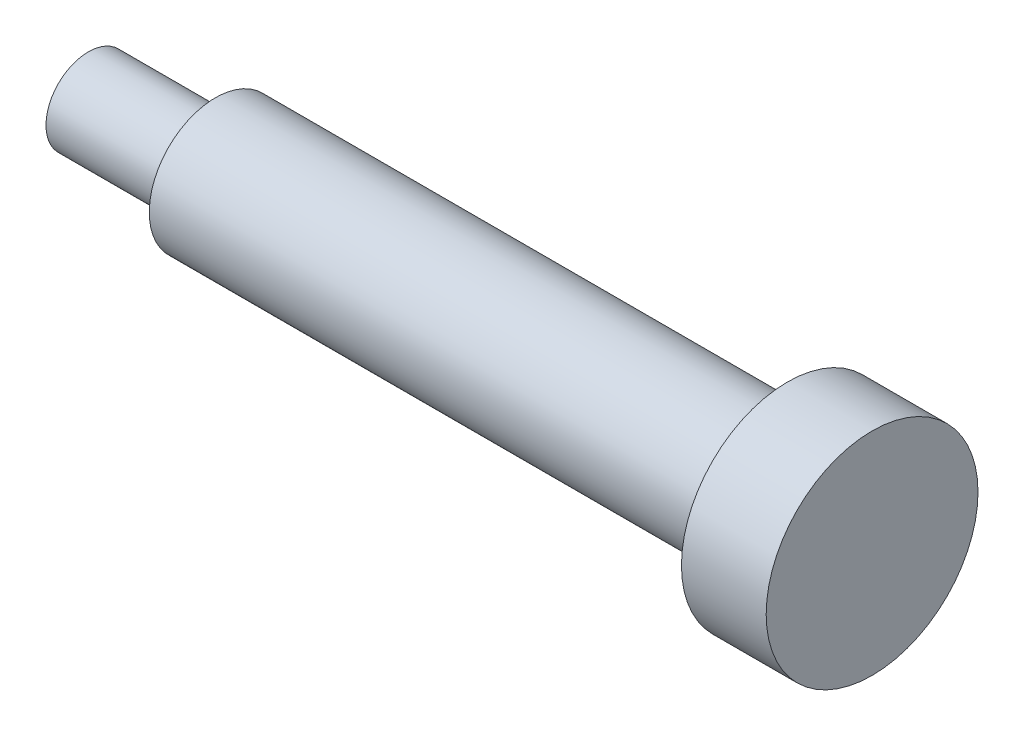
SolidWorks part; units mm, degrees
ref_plane "Front Plane" through (0, 0, 0) normal (0, 0, 1) x (1, 0, 0)
ref_plane "Top Plane" through (0, 0, 0) normal (0, 1, 0) x (1, 0, 0)
ref_plane "Right Plane" through (0, 0, 0) normal (1, 0, 0) x (0, 0, -1)
sketch "Sketch1" plane through (0, 0, 0) normal (0, 0, 1) x (1, 0, 0)
  line L0 (-18.5, 0) -> (18.5, 0) construction
  line L1 (-18.5, 0) -> (-18.5, 2)
  line L2 (-18.5, 2) -> (-12.5, 2)
  line L3 (-12.5, 0) -> (-12.5, 3.125)
  line L4 (-12.5, 3.125) -> (14.5, 3.125)
  line L5 (14.5, 0) -> (14.5, 5)
  line L6 (14.5, 5) -> (18.5, 5)
  line L7 (18.5, 5) -> (18.5, 0)
  point P4 (0, 0)
  dimension "D1" = 6
  dimension "D2" = 27
  dimension "D3" = 4
revolve "Revolve1" add sketch "Sketch1" angle 360 about L0
